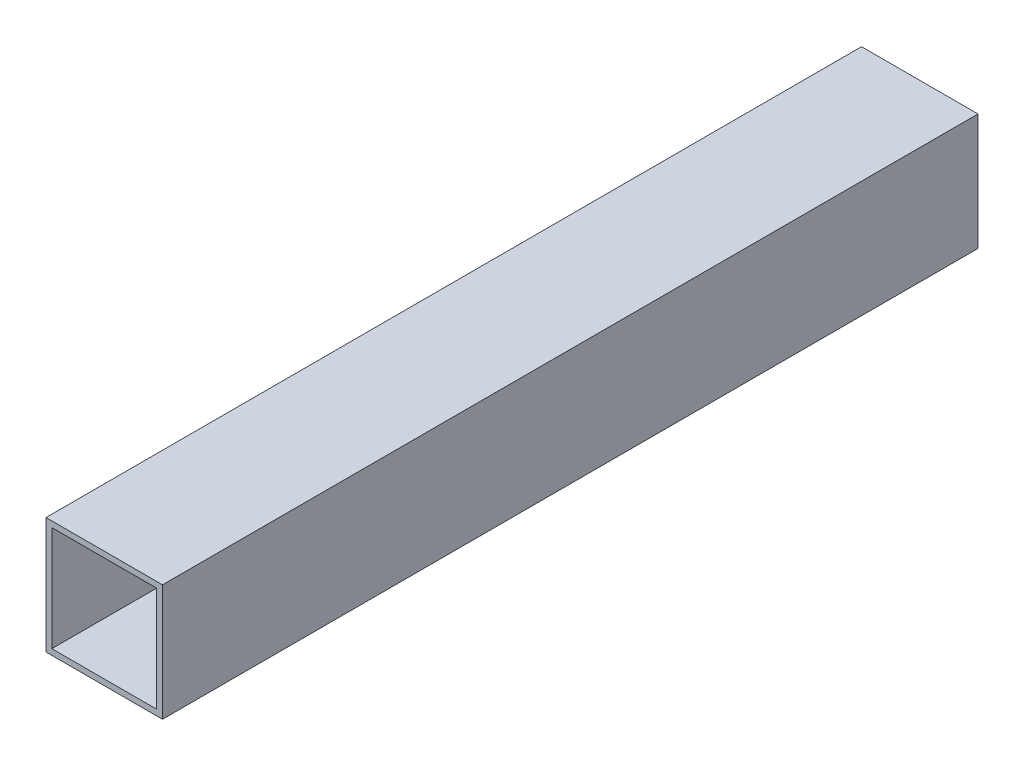
SolidWorks part; units mm, degrees
ref_plane "Front Plane" through (0, 0, 0) normal (0, 0, 1) x (1, 0, 0)
ref_plane "Top Plane" through (0, 0, 0) normal (0, 1, 0) x (1, 0, 0)
ref_plane "Right Plane" through (0, 0, 0) normal (1, 0, 0) x (0, 0, -1)
sketch "Sketch1" plane through (0, 0, 0) normal (0, 0, 1) x (1, 0, 0)
  line L1 (0, 0) -> (25.4, 0)
  line L2 (0, 0) -> (0, 25.4)
  line L3 (0, 25.4) -> (25.4, 25.4)
  line L4 (25.4, 0) -> (25.4, 25.4)
  dimension "D1" = 25.4
  dimension "D2" = 25.4
extrude "Boss-Extrude1" add sketch "Sketch1" along normal blind 177.8
sketch "Sketch2" plane through (0, 0, 177.8) normal (0, 0, 1) x (1, 0, 0)
  line L0 (25.4, 25.4) -> (0, 25.4) construction
  line L1 (1.27, 24.13) -> (24.13, 24.13)
  line L2 (1.27, 24.13) -> (1.27, 1.27)
  line L3 (1.27, 1.27) -> (24.13, 1.27)
  line L4 (24.13, 24.13) -> (24.13, 1.27)
  line L5 (25.4, 0) -> (25.4, 25.4) construction
  dimension "D1" = 22.86
  dimension "D2" = 22.86
  dimension "D3" = 1.27
  dimension "D4" = 1.27
extrude "Cut-Extrude1" cut sketch "Sketch2" against normal blind 177.8
